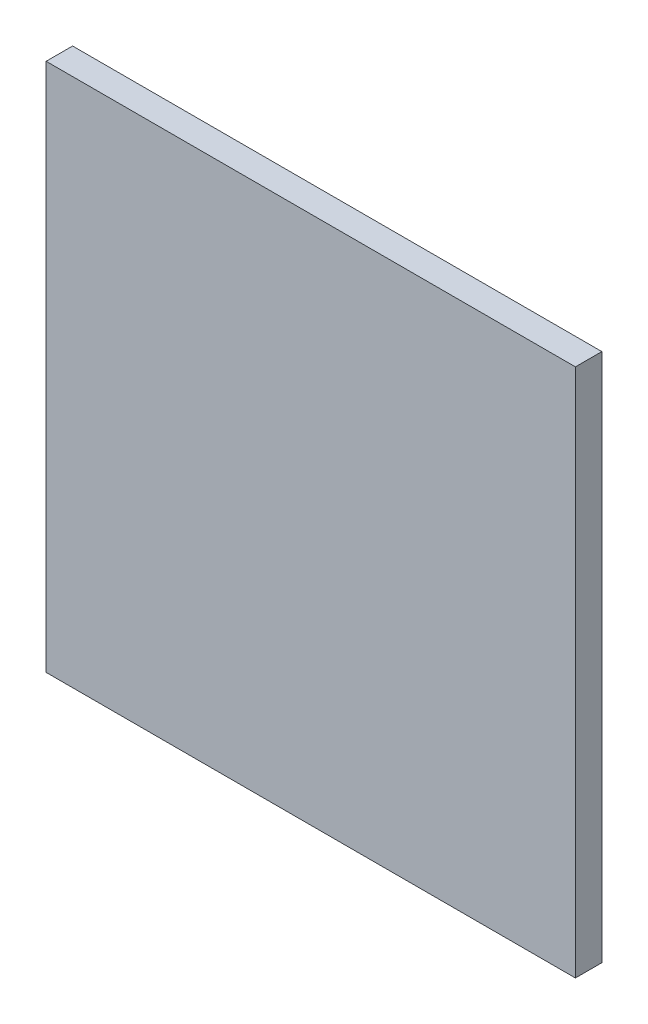
SolidWorks part; units mm, degrees
ref_plane "Front Plane" through (0, 0, 0) normal (0, 0, 1) x (1, 0, 0)
ref_plane "Top Plane" through (0, 0, 0) normal (0, 1, 0) x (1, 0, 0)
ref_plane "Right Plane" through (0, 0, 0) normal (1, 0, 0) x (0, 0, -1)
sketch "Sketch1" plane through (0, 0, 0) normal (0, 0, 1) x (1, 0, 0)
  line L1 (-2500, 2500) -> (2500, 2500)
  line L2 (-2500, 2500) -> (-2500, -2500)
  line L3 (-2500, -2500) -> (2500, -2500)
  line L4 (2500, 2500) -> (2500, -2500)
  line L5 (-2500, 2500) -> (2500, -2500) construction
  line L6 (-2500, -2500) -> (2500, 2500) construction
  point P0 (0, 0)
  dimension "D1" = 5000
  dimension "D2" = 5000
extrude "Boss-Extrude1" add sketch "Sketch1" along normal blind 250
